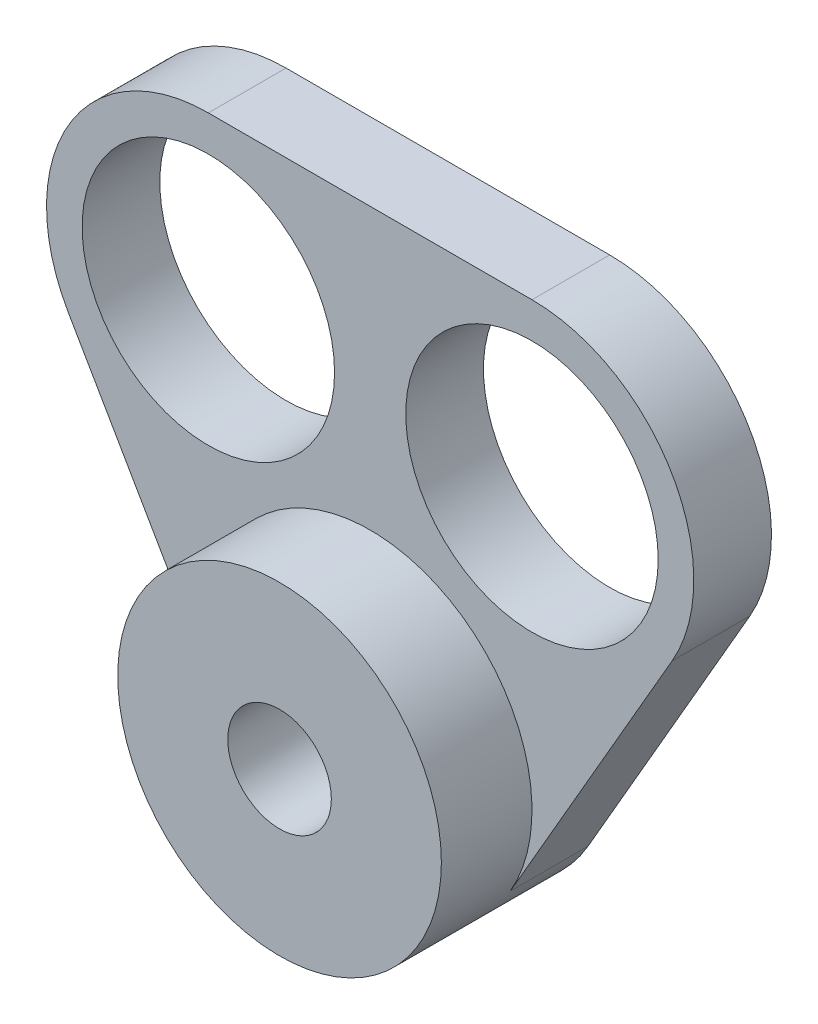
SolidWorks part; units mm, degrees
ref_plane "Alzado" through (0, 0, 0) normal (0, 0, 1) x (1, 0, 0)
ref_plane "Planta" through (0, 0, 0) normal (0, 1, 0) x (1, 0, 0)
ref_plane "Vista lateral" through (0, 0, 0) normal (1, 0, 0) x (0, 0, -1)
sketch "Croquis1" plane through (0, 0, 0) normal (0, 0, 1) x (1, 0, 0)
  line L0 (0, 0) -> (12.5, 21.6506) construction
  line L1 (12.5, 21.6506) -> (-12.5, 21.6506) construction
  line L2 (-12.5, 21.6506) -> (0, 0) construction
  line L3 (0, 0) -> (12.5, 21.6506) construction
  line L4 (12.5, 21.6506) -> (25.4113, 14.1963) construction
  line L5 (12.5, 21.6506) -> (0, 0) construction
  line L6 (0, 0) -> (14.6404, -8.4526) construction
  line L7 (10.8253, -6.25) -> (23.3253, 15.4006)
  line L8 (12.5, 21.6506) -> (-12.5, 21.6506) construction
  line L9 (-12.5, 21.6506) -> (-12.5, 40.0051) construction
  line L10 (12.5, 21.6506) -> (12.5, 40.0051) construction
  line L11 (-12.5, 34.1506) -> (12.5, 34.1506)
  line L12 (-12.5, 21.6506) -> (0, 0) construction
  line L13 (0, 0) -> (-19.3941, -11.1972) construction
  line L14 (0, 0) -> (-12.5, 21.6506) construction
  line L15 (-12.5, 21.6506) -> (-31.25, 10.8253) construction
  line L16 (-23.3253, 15.4006) -> (-10.8253, -6.25)
  circle A0 centre (-12.5, 21.6506) radius 12.5
  circle A1 centre (12.5, 21.6506) radius 12.5
  circle A2 centre (0, 0) radius 9.75
  circle A3 centre (-12.5, 21.6506) radius 9.75
  circle A4 centre (12.5, 21.6506) radius 9.75
  circle A5 centre (0, 0) radius 12.5
  dimension "D4" = 25
  dimension "D5" = 19.5
  dimension "D6" = 25
  dimension "D7" = 19.5
  dimension "D8" = 19.5
  dimension "D9" = 25
  dimension "D1" = 25
  dimension "D2" = 25
  dimension "D3" = 25
extrude "Saliente-Extruir1" add sketch "Croquis1" along normal blind 6 contours A0 A3 | A1 L11 A0 | A1 A4 | A5 A1 A0 | A5 A0 L16 | A5 A2 | A5 L7 A1
sketch "Croquis2" plane through (0, 0, 6) normal (0, 0, 1) x (1, 0, 0)
  circle A0 centre (0, 0) radius 12.5
  circle A1 centre (0, 0) radius 4
  dimension "D1" = 25
  dimension "D2" = 8
extrude "Saliente-Extruir3" add sketch "Croquis2" along normal blind 7
